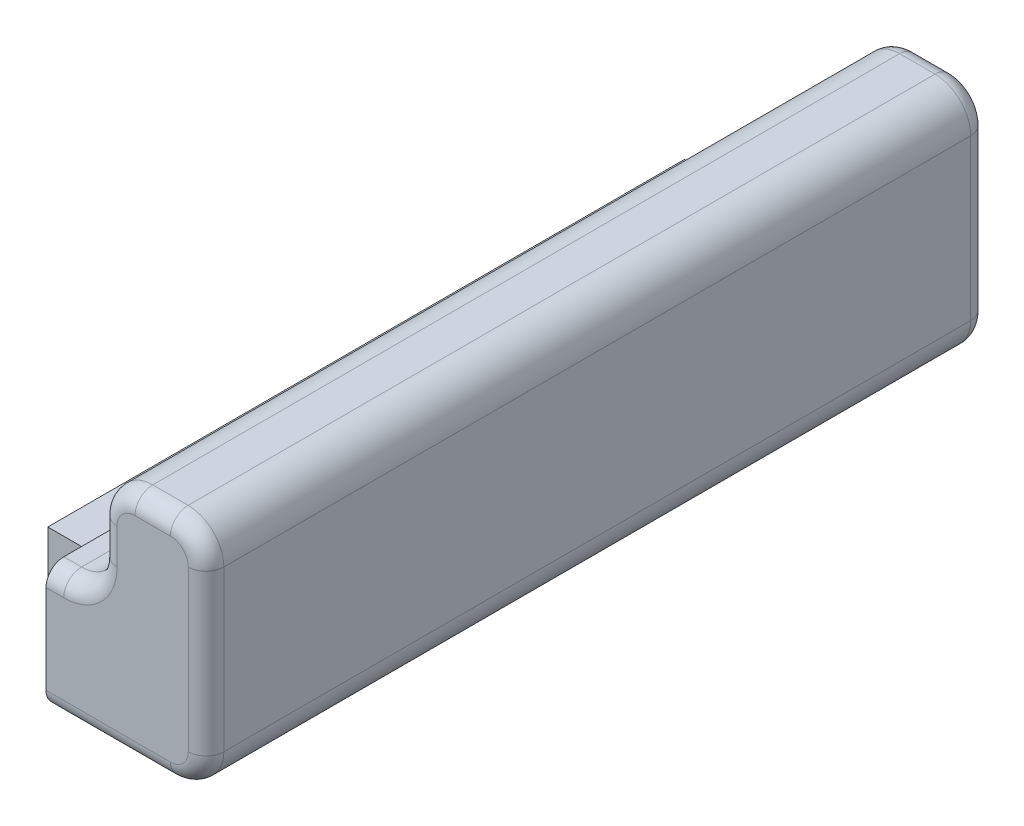
SolidWorks part; units mm, degrees
material "ABS"
ref_plane "Front Plane" through (0, 0, 0) normal (0, 0, 1) x (1, 0, 0)
ref_plane "Top Plane" through (0, 0, 0) normal (0, 1, 0) x (1, 0, 0)
ref_plane "Right Plane" through (0, 0, 0) normal (1, 0, 0) x (0, 0, -1)
sketch "Sketch1" plane through (0, 0, 0) normal (0, 0, 1) x (1, 0, 0)
  line L0 (-5.9507, -1.6677) -> (-5.4528, -1.6677)
  line L1 (-4.4507, -0.6656) -> (-4.4507, 0.3323)
  line L2 (-3.4486, 1.3344) -> (-2.4528, 1.3344)
  line L3 (-1.4507, 0.3323) -> (-1.4507, -4.1656)
  line L7 (-5.9507, -1.6677) -> (-5.9507, -5.1677)
  line L8 (-5.9507, -5.1677) -> (-2.4528, -5.1677)
  arc A0 (-1.4507, -4.1656) -> (-2.4528, -5.1677) centre (-2.4528, -4.1656) cw
  arc A1 (-2.4528, 1.3344) -> (-1.4507, 0.3323) centre (-2.4528, 0.3323) cw
  arc A2 (-4.4507, 0.3323) -> (-3.4486, 1.3344) centre (-3.4486, 0.3323) cw
  arc A3 (-5.4528, -1.6677) -> (-4.4507, -0.6656) centre (-5.4528, -0.6656) ccw
  dimension "D4" = 3
extrude "Boss-Extrude1" add sketch "Sketch1" along normal blind 22
fillet "Fillet1" radius 0.5 18 edges at (-5.7018, -1.6677, 22) (-4.7442, -1.3742, 22) (-2.9507, 1.3344, 22) (-4.1572, 1.0409, 22) (-4.4507, -0.1667, 22) (-1.7442, 1.0409, 22) (-1.4507, -1.9167, 22) (-1.7442, -4.8742, 22) (-5.7018, -1.6677, 0) (-4.4507, -0.1667, 0) (-4.7442, -1.3742, 0) (-4.1572, 1.0409, 0) (-2.9507, 1.3344, 0) (-1.7442, 1.0409, 0) (-1.4507, -1.9167, 0) (-1.7442, -4.8742, 0) (-4.2018, -5.1677, 22) (-4.2018, -5.1677, 0)
sketch "Sketch2" plane through (-5.9507, 0, 0) normal (-1, 0, 0) x (0, 0, 1)
  line L1 (2.05, -2.7177) -> (19.95, -2.7177)
  line L2 (2.05, -2.7177) -> (2.05, -4.1177)
  line L3 (2.05, -4.1177) -> (19.95, -4.1177)
  line L4 (19.95, -2.7177) -> (19.95, -4.1177)
  line L10 (21.5, -1.6677) -> (0.5, -1.6677) construction
  line L11 (21.5, -5.1677) -> (0.5, -5.1677) construction
  line L12 (22, -2.1677) -> (22, -4.6677) construction
  line L13 (0, -2.1677) -> (0, -4.6677) construction
  dimension "D1" = 1.05
  dimension "D2" = 1.05
  dimension "D3" = 2.05
  dimension "D4" = 2.05
extrude "Boss-Extrude2" add sketch "Sketch2" along normal blind 2
